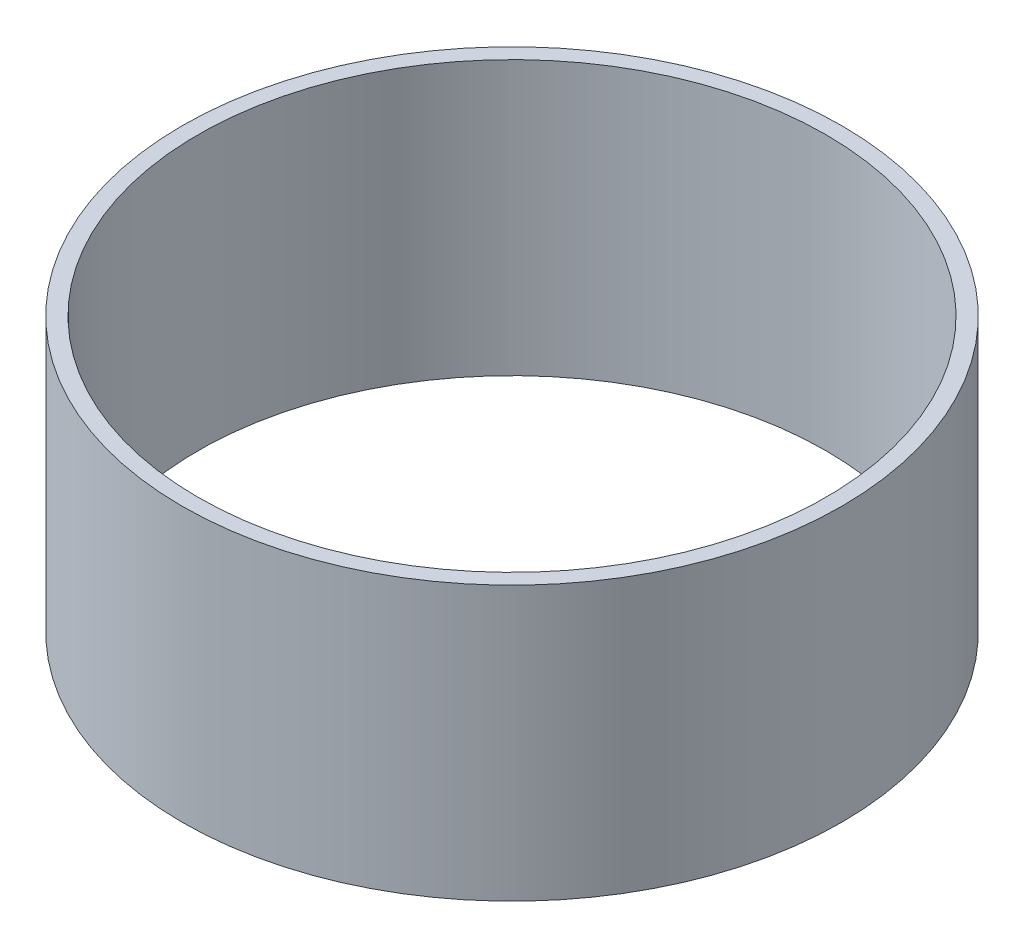
SolidWorks part; units mm, degrees
ref_plane "Спереди" through (0, 0, 0) normal (0, 0, 1) x (1, 0, 0)
ref_plane "Сверху" through (0, 0, 0) normal (0, 1, 0) x (1, 0, 0)
ref_plane "Справа" through (0, 0, 0) normal (1, 0, 0) x (0, 0, -1)
sketch "Эскиз1" plane through (0, 0, 0) normal (0, 1, 0) x (1, 0, 0)
  circle A0 centre (0, 0) radius 63
extrude "Бобышка-Вытянуть1" add sketch "Эскиз1" along normal blind 52.3
sketch "Эскиз2" plane through (0, 52.3, 0) normal (0, 1, 0) x (1, 0, 0)
  circle A0 centre (0, 0) radius 60
extrude "Вырез-Вытянуть1" cut sketch "Эскиз2" against normal blind 52.3
